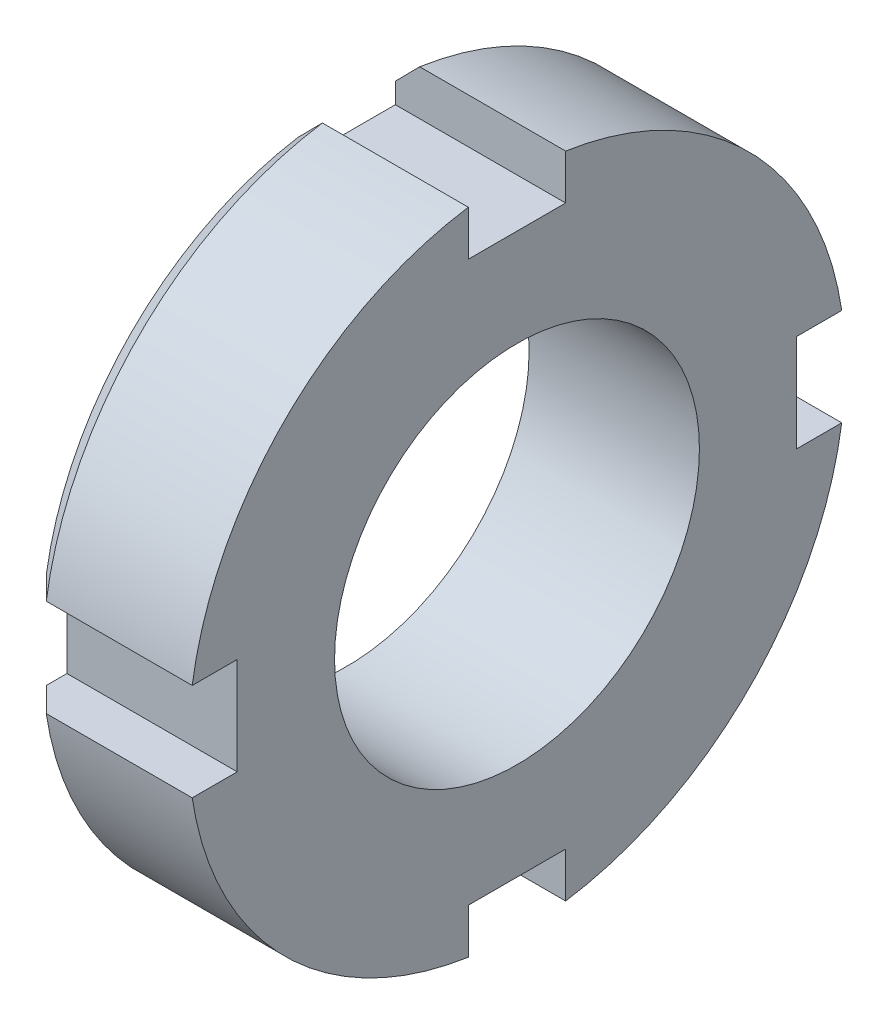
SolidWorks part; units mm, degrees
ref_plane "Front Plane" through (0, 0, 0) normal (0, 0, 1) x (1, 0, 0)
ref_plane "Top Plane" through (0, 0, 0) normal (0, 1, 0) x (1, 0, 0)
ref_plane "Right Plane" through (0, 0, 0) normal (1, 0, 0) x (0, 0, -1)
sketch "Sketch1" plane through (0, 0, 0) normal (1, 0, 0) x (0, 0, -1)
  circle A0 centre (0, 0) radius 13.5
  dimension "D1" = 27
extrude "Boss-Extrude1" add sketch "Sketch1" along normal blind 7
sketch "Sketch2" plane through (7, 0, 0) normal (1, 0, 0) x (0, 0, -1)
  circle A0 centre (0, 0) radius 7.5
  dimension "D1" = 15
extrude "Cut-Extrude1" cut sketch "Sketch2" against normal through all
chamfer "Chamfer1" distance 1 angle 45 1 edges at (0, 0, -13.5)
sketch "Sketch3" plane through (7, 0, 0) normal (1, 0, 0) x (0, 0, -1)
  line L0 (0, 0) -> (0, 13.9129) construction
  line L2 (-2, 15.5) -> (2, 15.5)
  line L3 (-2, 15.5) -> (-2, 11.5)
  line L4 (-2, 11.5) -> (2, 11.5)
  line L5 (2, 15.5) -> (2, 11.5)
  line L6 (-2, 15.5) -> (2, 11.5) construction
  line L7 (-2, 11.5) -> (2, 15.5) construction
  circle A0 centre (0, 0) radius 13.5 construction
  point P3 (0, 13.5)
  dimension "D1" = 4
  dimension "D2" = 4
extrude "Cut-Extrude2" cut sketch "Sketch3" against normal through all
pattern_circular "CirPattern1" count 4 over 360 about axis through (0, 0, 0) along (1, 0, 0) of "Cut-Extrude2"
